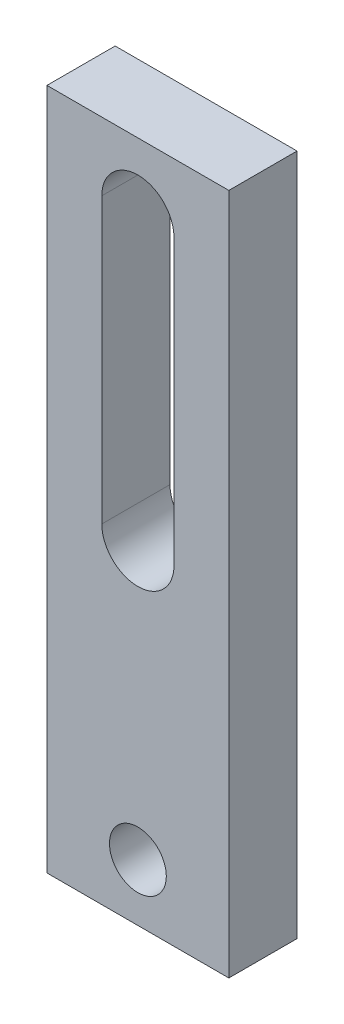
SolidWorks part; units mm, degrees
ref_plane "Front Plane" through (0, 0, 0) normal (0, 0, 1) x (1, 0, 0)
ref_plane "Top Plane" through (0, 0, 0) normal (0, 1, 0) x (1, 0, 0)
ref_plane "Right Plane" through (0, 0, 0) normal (1, 0, 0) x (0, 0, -1)
sketch "Sketch1" plane through (0, 0, 0) normal (0, 0, 1) x (1, 0, 0)
  line L1 (-22.117, 0) -> (-14.117, 0)
  line L2 (-22.117, 0) -> (-22.117, 30)
  line L3 (-22.117, 30) -> (-14.117, 30)
  line L4 (-14.117, 0) -> (-14.117, 30)
  dimension "D1" = 8
  dimension "D2" = 30
extrude "Boss-Extrude1" add sketch "Sketch1" along normal blind 3
sketch "Sketch2" plane through (0, 0, 3) normal (0, 0, 1) x (1, 0, 0)
  line L0 (-22.117, 0) -> (-14.117, 0) construction
  line L1 (-16.5295, 27) -> (-16.5295, 14.5)
  line L2 (-19.7045, 27) -> (-19.7045, 14.5)
  circle A0 centre (-18.117, 2.5) radius 1.25
  arc A1 (-19.7045, 27) -> (-16.5295, 27) centre (-18.117, 27) cw
  arc A2 (-19.7045, 14.5) -> (-16.5295, 14.5) centre (-18.117, 14.5) ccw
  dimension "D1" = 2.5
extrude "Cut-Extrude1" cut sketch "Sketch2" against normal blind 3
